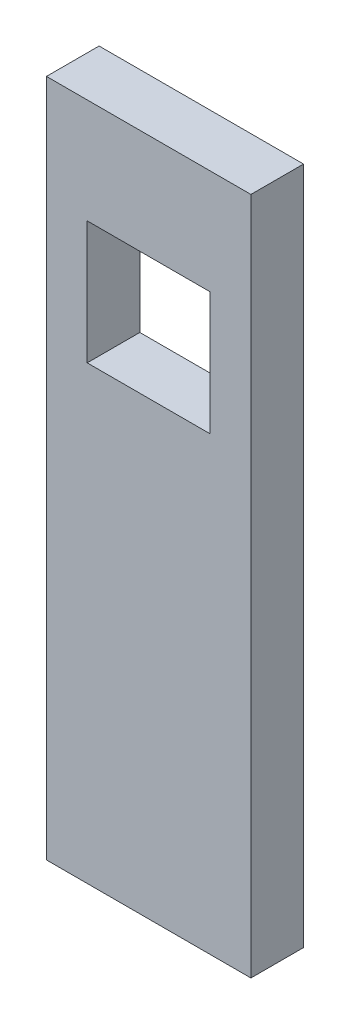
SolidWorks part; units mm, degrees
ref_plane "Front Plane" through (0, 0, 0) normal (0, 0, 1) x (1, 0, 0)
ref_plane "Top Plane" through (0, 0, 0) normal (0, 1, 0) x (1, 0, 0)
ref_plane "Right Plane" through (0, 0, 0) normal (1, 0, 0) x (0, 0, -1)
sketch "Sketch1" plane through (0, 0, 0) normal (0, 0, 1) x (1, 0, 0)
  line L0 (0, 66.85) -> (0, 44.55) construction
  line L1 (0, 66.85) -> (20, 66.85) construction
  line L2 (0, 44.55) -> (0, 39.4) construction
  line L3 (20, 0) -> (0, 0) construction
  line L4 (4.025, 56.5) -> (15.975, 56.5) construction
  line L5 (4.025, 44.55) -> (15.975, 44.55) construction
  line L6 (4.025, 56.5) -> (4.025, 44.55) construction
  line L7 (15.975, 56.5) -> (15.975, 44.55) construction
  line L8 (0, 44.55) -> (20, 44.55) construction
  line L9 (0, 39.4) -> (20, 39.4) construction
  line L10 (0, 39.4) -> (0, 27.45) construction
  line L11 (0, 27.45) -> (0, 22.3) construction
  line L12 (20, 44.55) -> (20, 39.4) construction
  line L13 (20, 66.85) -> (20, 44.55) construction
  line L14 (0, 22.3) -> (0, 0) construction
  line L15 (20, 39.4) -> (20, 27.45) construction
  line L16 (20, 27.45) -> (20, 22.3) construction
  line L17 (20, 22.3) -> (20, 0) construction
  line L18 (0, 27.45) -> (20, 27.45) construction
  line L19 (20, 22.3) -> (0, 22.3) construction
  line L20 (10, -0.0005) -> (10, 4.0956) construction
  line L21 (-0.1, 66.95) -> (20.1, 66.95)
  line L22 (20.1, 66.95) -> (20.1, 44.55)
  line L23 (20.1, 44.55) -> (20.1, 39.4)
  line L24 (20.1, 39.4) -> (20.1, 27.45)
  line L25 (20.1, 27.45) -> (20.1, 22.3)
  line L26 (20.1, 22.3) -> (20.1, -0.1)
  line L27 (20.1, -0.1) -> (-0.1, -0.1)
  line L28 (-0.1, 22.3) -> (-0.1, -0.1)
  line L29 (-0.1, 27.45) -> (-0.1, 22.3)
  line L30 (-0.1, 39.4) -> (-0.1, 27.45)
  line L31 (-0.1, 44.55) -> (-0.1, 39.4)
  line L32 (-0.1, 66.95) -> (-0.1, 44.55)
  line L33 (3.925, 56.6) -> (16.075, 56.6)
  line L34 (16.075, 56.6) -> (16.075, 44.45)
  line L35 (3.925, 44.45) -> (16.075, 44.45)
  line L36 (3.925, 56.6) -> (3.925, 44.45)
  point P18 (10, 44.55)
  point P20 (10, 56.5)
  point P21 (10, 66.85)
  dimension "D1" = 22.3
  dimension "D2" = 11.95
  dimension "D3" = 5.15
  dimension "D4" = 20
  dimension "D5" = 11.95
  dimension "D6" = 11.95
  dimension "D7" = 0.1
extrude "Boss-Extrude1" add sketch "Sketch1" along normal mid plane 5.2
